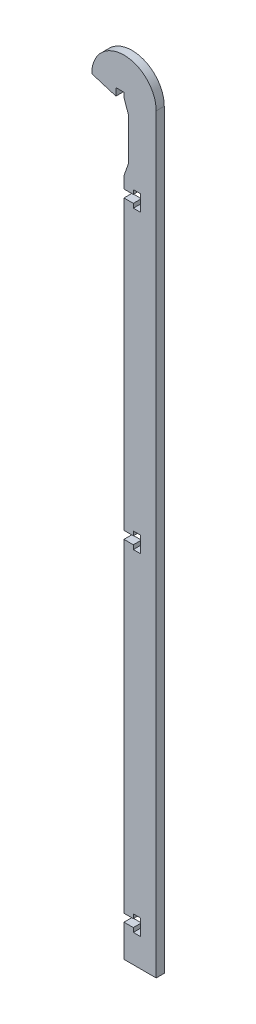
SolidWorks part; units mm, degrees
ref_plane "Front Plane" through (0, 0, 0) normal (0, 0, 1) x (1, 0, 0)
ref_plane "Top Plane" through (0, 0, 0) normal (0, 1, 0) x (1, 0, 0)
ref_plane "Right Plane" through (0, 0, 0) normal (1, 0, 0) x (0, 0, -1)
sketch "Sketch1" plane through (0, 0, 0) normal (0, 0, 1) x (1, 0, 0)
  line L0 (0, 0) -> (0, -1.8034)
  line L1 (0, -295.91) -> (12.7, -295.91)
  line L2 (12.7, -295.91) -> (12.7, 0)
  line L3 (0, -1.8034) -> (1.778, -6.8834)
  line L4 (0, 0) -> (-3.175, 0)
  line L5 (-3.175, 0) -> (-3.175, -2.921)
  line L6 (-3.175, -2.921) -> (-12.7, 0)
  line L7 (0, -33.02) -> (3.683, -33.02)
  line L8 (3.683, -33.02) -> (3.683, -31.369)
  line L9 (3.683, -31.369) -> (6.477, -31.369)
  line L10 (6.477, -31.369) -> (6.477, -37.719)
  line L11 (6.477, -37.719) -> (3.683, -37.719)
  line L12 (3.683, -37.719) -> (3.683, -36.068)
  line L13 (3.683, -36.068) -> (0, -36.068)
  line L14 (0, -280.162) -> (3.683, -280.162)
  line L15 (3.683, -280.162) -> (3.683, -278.511)
  line L16 (3.683, -278.511) -> (6.477, -278.511)
  line L17 (6.477, -278.511) -> (6.477, -284.861)
  line L18 (6.477, -284.861) -> (3.683, -284.861)
  line L19 (3.683, -284.861) -> (3.683, -283.21)
  line L20 (3.683, -283.21) -> (0, -283.21)
  line L21 (0, -28.4734) -> (0, -33.02)
  line L22 (0, -283.21) -> (0, -295.91)
  line L23 (1.778, -6.8834) -> (1.778, -23.3934)
  line L24 (1.778, -23.3934) -> (0, -28.4734)
  line L25 (0, -36.068) -> (0, -149.5213)
  line L26 (0, -152.5693) -> (3.683, -152.5693)
  line L27 (3.683, -152.5693) -> (3.683, -154.2203)
  line L28 (3.683, -154.2203) -> (6.477, -154.2203)
  line L29 (6.477, -154.2203) -> (6.477, -147.8703)
  line L30 (6.477, -147.8703) -> (3.683, -147.8703)
  line L31 (3.683, -147.8703) -> (3.683, -149.5213)
  line L32 (3.683, -149.5213) -> (0, -149.5213)
  line L33 (0, -152.5693) -> (0, -280.162)
  arc A0 (-12.7, 0) -> (12.7, 0) centre (0, 0) cw
  dimension "D1" = 12.7
  dimension "D2" = 295.91
  dimension "D3" = 6.35
  dimension "D4" = 2.921
  dimension "D5" = 3.175
  dimension "D6" = 2.794
  dimension "D7" = 6.477
  dimension "D8" = 3.048
  dimension "D9" = 33.02
  dimension "D10" = 12.7
  dimension "D11" = 5.08
  dimension "D12" = 6.8834
  dimension "D13" = 16.51
  dimension "D14" = 5.08
  dimension "D15" = 1.778
  dimension "D16" = 149.5213
extrude "Boss-Extrude1" add sketch "Sketch1" along normal blind 3.175
